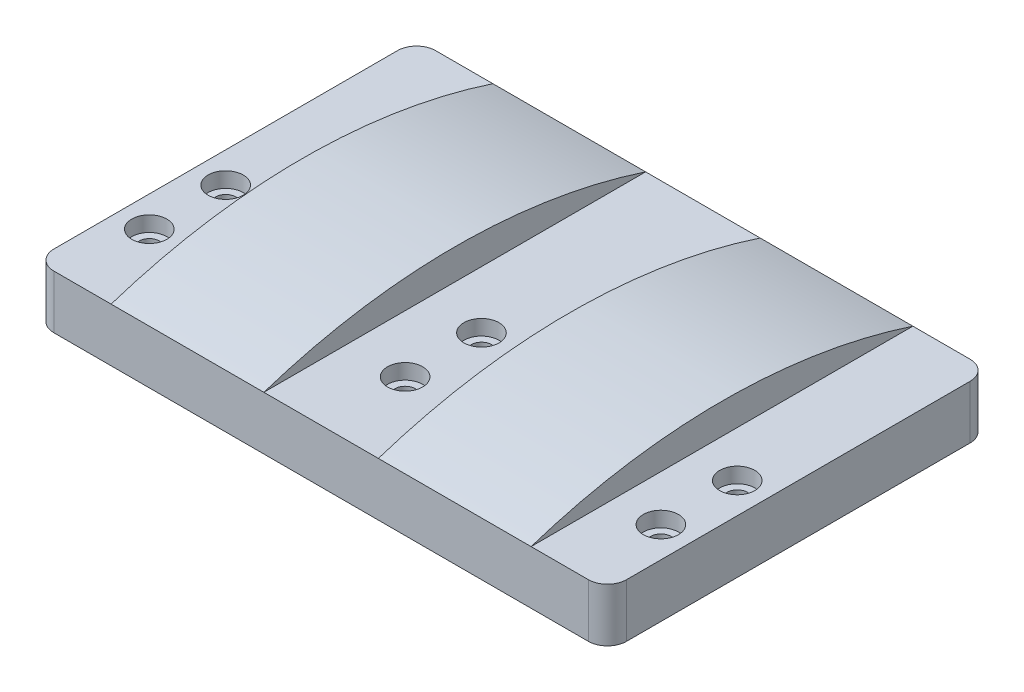
SolidWorks part; units mm, degrees
ref_plane "Front Plane" through (0, 0, 0) normal (0, 0, 1) x (1, 0, 0)
ref_plane "Top Plane" through (0, 0, 0) normal (0, 1, 0) x (1, 0, 0)
ref_plane "Right Plane" through (0, 0, 0) normal (1, 0, 0) x (0, 0, -1)
sketch "Sketch1" plane through (0, 0, 0) normal (0, 1, 0) x (1, 0, 0)
  line L0 (0, 60) -> (150, 60) construction
  line L1 (0, 0) -> (150, 0)
  line L2 (0, 0) -> (0, 100)
  line L3 (0, 100) -> (150, 100)
  line L4 (150, 0) -> (150, 100)
  line L5 (0, 0) -> (150, 100) construction
  line L6 (0, 100) -> (150, 0) construction
  point P4 (75, 50)
  dimension "D1" = 150
  dimension "D2" = 60
  dimension "D3" = 40
extrude "Boss-Extrude1" add sketch "Sketch1" along normal blind 14
sketch "Sketch2" plane through (0, 14, 0) normal (0, 1, 0) x (1, 0, 0)
  line L0 (8, 42) -> (142, 42) construction
  line L1 (0, 0) -> (150, 0) construction
  line L2 (75, 100) -> (75, 42) construction
  line L3 (150, 100) -> (0, 100) construction
  line L4 (75, 42) -> (75, 0) construction
  line L5 (0, 100) -> (0, 0) construction
  line L6 (43.5648, 100) -> (43.5648, 85) construction
  line L7 (43.5648, 85) -> (43.5648, 42) construction
  line L8 (8, 32) -> (142, 32) construction
  circle A0 centre (8, 42) radius 2.65
  circle A1 centre (142, 42) radius 2.65
  circle A2 centre (75, 42) radius 2.65
  circle A3 centre (142, 22) radius 2.65
  circle A4 centre (75, 22) radius 2.65
  circle A5 centre (8, 22) radius 2.65
  dimension "D2" = 5.3
  dimension "D1" = 15
  dimension "D3" = 8
  dimension "D4" = 43
  dimension "D5" = 10
extrude "Cut-Extrude1" cut sketch "Sketch2" against normal through all
sketch "Sketch3" plane through (0, 0, 0) normal (-1, 0, 0) x (0, 0, 1)
  line L1 (-100, 0) -> (-80.95, 0)
  line L2 (-100, 0) -> (-100, -1)
  line L3 (-100, -1) -> (-80.95, -1)
  line L4 (-80.95, 0) -> (-80.95, -1)
  line L5 (-100, 0) -> (-80.95, -1) construction
  line L6 (-100, -1) -> (-80.95, 0) construction
  point P4 (-90.475, -0.5)
  dimension "D1" = 19.05
  dimension "D2" = 1
sketch "Sketch4" plane through (0, 14, 0) normal (0, 1, 0) x (1, 0, 0)
  circle A0 centre (8, 42) radius 4.6
  circle A1 centre (75, 42) radius 4.6
  circle A2 centre (142, 42) radius 4.6
  circle A3 centre (8, 22) radius 4.6
  circle A4 centre (75, 22) radius 4.6
  circle A5 centre (142, 22) radius 4.6
  dimension "D1" = 9.2
extrude "Cut-Extrude2" cut sketch "Sketch4" against normal blind 4
ref_plane "Plane1" through (75, 0, 0) normal (1, 0, 0) x (0, 0, -1)
sketch "Sketch6" plane through (75, 0, 0) normal (1, 0, 0) x (0, 0, -1)
  line L0 (50, 22) -> (50, 14) construction
  line L1 (0, 14) -> (100, 14) construction
  line L2 (0, 14) -> (100, 14)
  arc A0 (0, 14) -> (100, 14) centre (50, -138.25) cw
  dimension "D1" = 8
extrude "Boss-Extrude3" add sketch "Sketch6" along normal blind 40 from offset 15 contours L0 A0 L2 | A0 L0 L2
mirror "Mirror1" about plane through (75, 0, 0) normal (1, 0, 0) of "Boss-Extrude3"
fillet "Fillet1" radius 5 4 edges at (150, 7, -100) (0, 7, -100) (0, 7, 0) (150, 7, 0)
